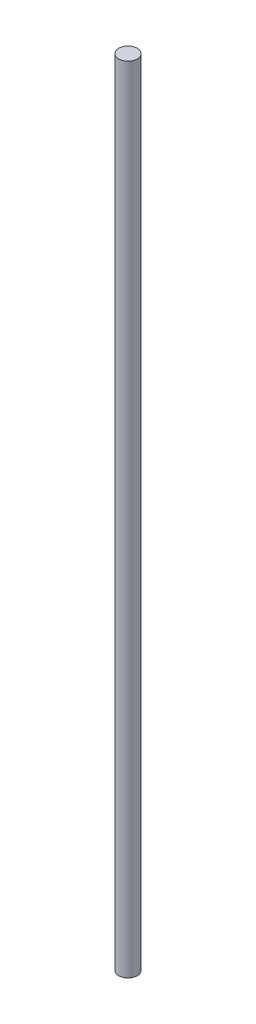
SolidWorks part; units mm, degrees
ref_plane "Front Plane" through (0, 0, 0) normal (0, 0, 1) x (1, 0, 0)
ref_plane "Top Plane" through (0, 0, 0) normal (0, 1, 0) x (1, 0, 0)
ref_plane "Right Plane" through (0, 0, 0) normal (1, 0, 0) x (0, 0, -1)
sketch "Sketch1" plane through (0, 0, 0) normal (0, 1, 0) x (1, 0, 0)
  circle A0 centre (0, 0) radius 2.3813
  dimension "D1" = 4.7625
extrude "Boss-Extrude1" add sketch "Sketch1" along normal blind 203.2
